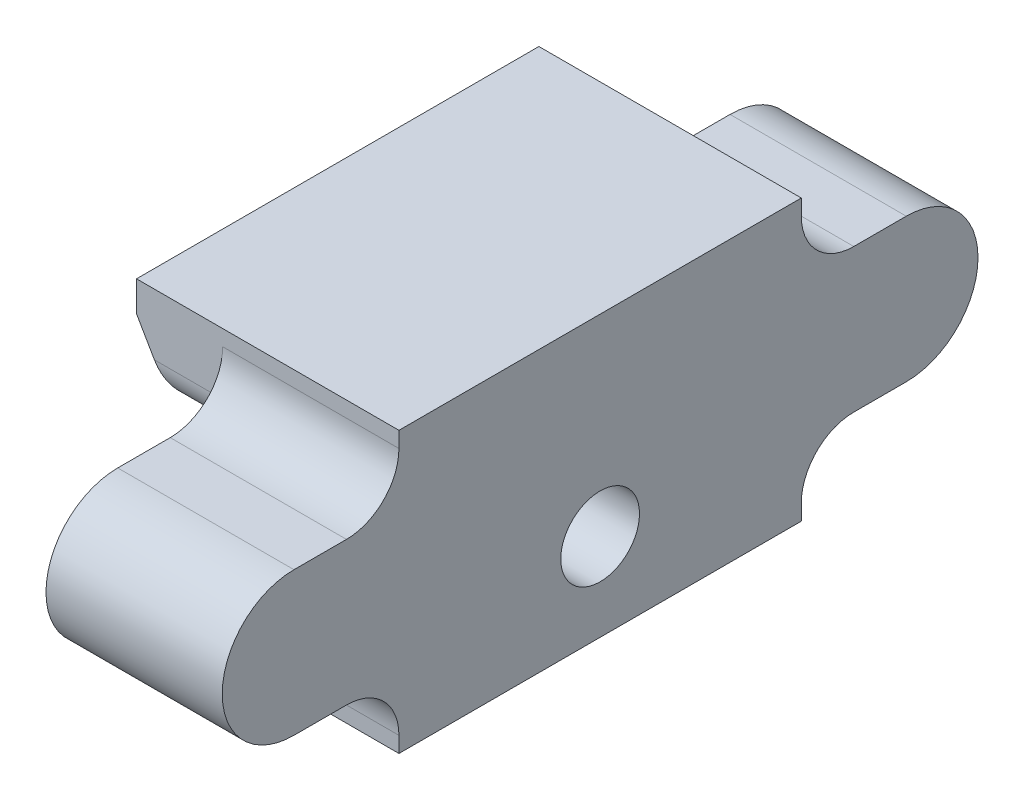
SolidWorks part; units mm, degrees
material "Сплав 2024"
ref_plane "Спереди" through (0, 0, 0) normal (0, 0, 1) x (1, 0, 0)
ref_plane "Сверху" through (0, 0, 0) normal (0, 1, 0) x (1, 0, 0)
ref_plane "Справа" through (0, 0, 0) normal (1, 0, 0) x (0, 0, -1)
sketch "Эскиз1" plane through (0, 0, 0) normal (0, 0, 1) x (1, 0, 0)
  line L1 (0, 0) -> (-10.0746, 0)
  line L2 (-12.8246, 10.5) -> (-16, 16)
  line L3 (-16, 16) -> (0, 16)
  line L4 (0, 16) -> (0, 0)
  line L5 (-12.8246, 10.5) -> (-10.0746, 10.5)
  line L6 (-10.0746, 10.5) -> (-10.0746, 0)
  dimension "D2" = 5.5
  dimension "D3" = 16
  dimension "D4" = 60
  dimension "D6" = 16
extrude "Бобышка-Вытянуть1" add sketch "Эскиз1" along normal blind 23
sketch "Эскиз2" plane through (-10.0746, 0, 0) normal (1, 0, 0) x (0, 0, -1)
  line L0 (-23, 5) -> (0, 5) construction
  line L1 (-23, 0) -> (-23, 16) construction
  line L2 (0, 0) -> (0, 16) construction
  line L3 (-23, 0) -> (0, 0) construction
  line L4 (-19, 0) -> (-19, 16) construction
  line L5 (-23, 16) -> (0, 16) construction
  line L6 (-4, 16) -> (-4, 0) construction
  line L7 (-11.5, 16) -> (-11.5, 0) construction
  circle A0 centre (-19, 5) radius 2.5
  circle A1 centre (-4, 5) radius 2.5
  dimension "D4" = 5
  dimension "D1" = 5
  dimension "D2" = 7.5
extrude "Вырез-Вытянуть1" cut sketch "Эскиз2" along normal blind 4 and the other way through all
hole_wizard "Отверстие с зазором M41" positions "Эскиз4" profile "Эскиз3" hole size "M4" standard "Din" end condition through all
sketch "Эскиз4" plane through (0, 1.5428, 4.5254) normal (-1, 0, 0) x (0, 0, 1)
  line L0 (18.4746, 3.4572) -> (-4.5254, 3.4572) construction
  line L1 (6.9746, 14.4572) -> (6.9746, -1.5428) construction
  point P0 (6.9746, 3.4572)
sketch "Эскиз3" plane through (0, 5, 11.5) normal (0, 1, 0) x (0, 0, -1)
  line L0 (0, 0) -> (0, 16)
  line L1 (0, 16) -> (2.25, 16)
  line L2 (2.25, 16) -> (2.25, 0)
  line L5 (2.25, 0) -> (0, 0)
  line L11 (0, -6.35) -> (0, 107.95) construction
  dimension "Диаметр сквозного отверстия" = 4.5
  dimension "Глубина сквозного отверстия" = 16
chamfer "Фаска1" distance 1 angle 90 1 edges at (-16, 16, 11.5)
sketch "Эскиз7" plane through (0, 0, 0) normal (-1, 0, 0) x (0, 0, 1)
  line L0 (23, 8) -> (0, 8) construction
  line L2 (-6, 12.1) -> (0, 12.1)
  line L3 (0, 10.5) -> (0, 0) construction
  line L4 (0, 12.1) -> (0, 3.9)
  line L5 (0, 3.9) -> (-6, 3.9)
  line L6 (11.5, 0) -> (11.5, 9.35) construction
  line L7 (23, 0) -> (0, 0) construction
  line L8 (23, 0) -> (23, 16) construction
  line L9 (23, 12.1) -> (23, 3.9)
  line L10 (29, 12.1) -> (23, 12.1)
  line L11 (23, 3.9) -> (29, 3.9)
  arc A0 (-6, 12.1) -> (-6, 3.9) centre (-6, 8) ccw
  arc A1 (29, 12.1) -> (29, 3.9) centre (29, 8) cw
  point P8 (0, 8)
  dimension "D2" = 4.1
  dimension "D1" = 6
extrude "Бобышка-Вытянуть2" add sketch "Эскиз7" along normal up to surface (10.0746 mm away) up to face at (-10.0746, 7.25, 11.5)
fillet "Скругление1" radius 3 4 edges
fillet "Скругление2" radius 2 2 edges
sketch "Эскиз11" plane through (-10.0746, 0, 0) normal (-1, 0, 0) x (0, 0, 1)
  line L0 (-10.1, 12.8239) -> (-10.1, 1.9255) construction
  line L1 (23, 0) -> (0, 0) construction
  arc A0 (-6, 12.1) -> (-6, 3.9) centre (-6, 8) ccw construction
  point P5 (-10.1, 0)
